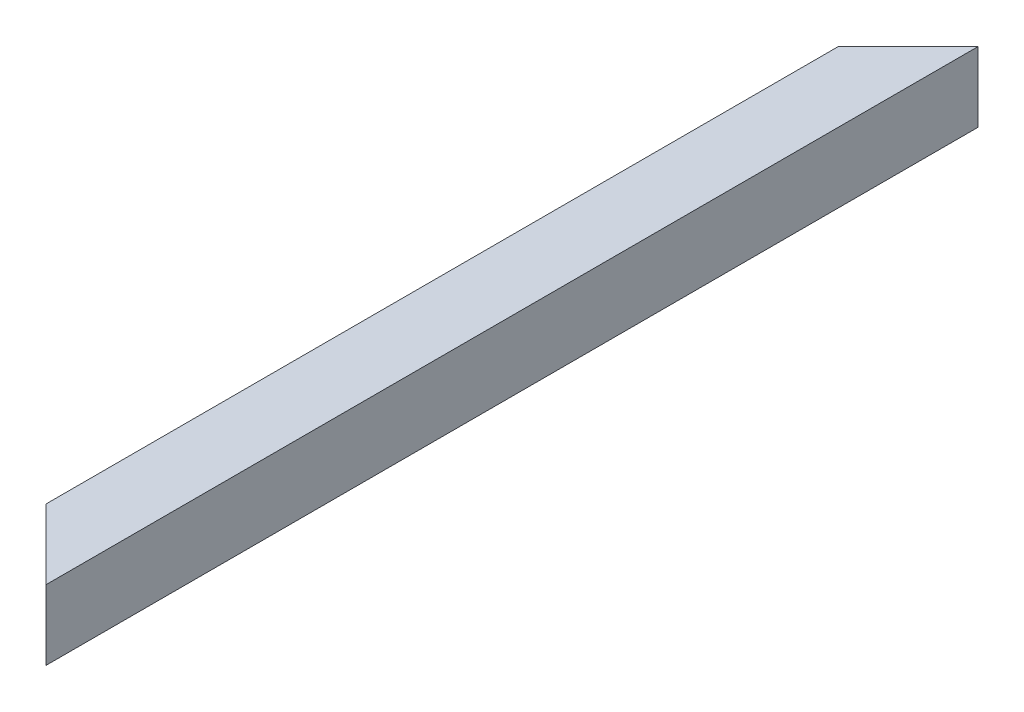
SolidWorks part; units mm, degrees
material "1.0037 (S235JR)"
ref_plane "Front Plane" through (0, 0, 0) normal (0, 0, 1) x (1, 0, 0)
ref_plane "Top Plane" through (0, 0, 0) normal (0, 1, 0) x (1, 0, 0)
ref_plane "Right Plane" through (0, 0, 0) normal (1, 0, 0) x (0, 0, -1)
curve "Curve1"
  spline degree 1 poles (0, 0, 0) (0, 0, 800) knots 0 0 1 1
sketch "Sketch1" plane through (0, 0, 0) normal (0, 0, 1) x (1, 0, 0)
  line L0 (0, 35.3535) -> (0, -33.8384) construction
  line L1 (-30, 30) -> (30, 30)
  line L2 (-30, 30) -> (-30, -30)
  line L3 (-30, -30) -> (30, -30)
  line L4 (30, 30) -> (30, -30)
  line L5 (-26, 26) -> (26, 26)
  line L6 (-26, 26) -> (-26, -26)
  line L7 (-26, -26) -> (26, -26)
  line L8 (26, 26) -> (26, -26)
  line L9 (-39.3939, 0) -> (41.5152, 0) construction
  dimension "D1" = 60
  dimension "D2" = 52
sweep "Sweep1" add profiles "Sketch1" path "Curve1"
sketch "Sketch2" plane through (0, 30, 0) normal (0, 1, 0) x (1, 0, 0)
  line L0 (30, 0) -> (-30, -60)
  line L1 (-30, 0) -> (-30, -800) construction
  line L2 (-30, -60) -> (-30, 0)
  line L3 (-30, 0) -> (30, 0)
  line L4 (30, -800) -> (-30, -740)
  line L5 (-30, -740) -> (-30, -800)
  line L6 (-30, -800) -> (30, -800)
  dimension "D1" = 45
  dimension "D2" = 45
extrude "Cut-Extrude1" cut sketch "Sketch2" against normal through all
